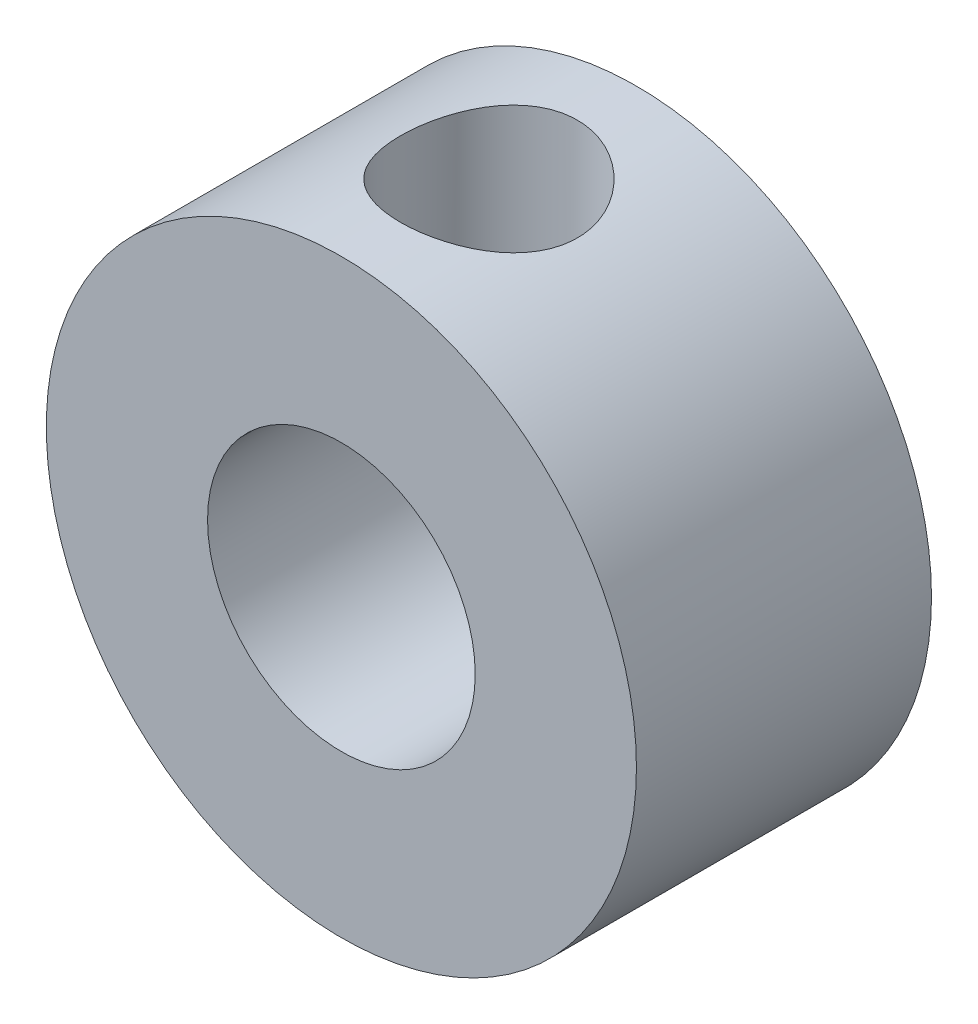
SolidWorks part; units mm, degrees
material "Plain Carbon Steel"
ref_plane "Front Plane" through (0, 0, 0) normal (0, 0, 1) x (1, 0, 0)
ref_plane "Top Plane" through (0, 0, 0) normal (0, 1, 0) x (1, 0, 0)
ref_plane "Right Plane" through (0, 0, 0) normal (1, 0, 0) x (0, 0, -1)
sketch "Sketch1" plane through (0, 0, 0) normal (0, 0, 1) x (1, 0, 0)
  circle A0 centre (0, 0) radius 3.175
  circle A1 centre (0, 0) radius 7
  dimension "D1" = 6.35
  dimension "D2" = 14
extrude "Boss-Extrude1" add sketch "Sketch1" along normal blind 7
ref_plane "Plane1" through (0, 7, 0) normal (0, 1, 0) x (1, 0, 0)
hole_wizard "M5x0.8 Tapped Hole1" positions "Sketch3" profile "Sketch2" tap size "M5x0.8" standard "ANSI Metric"
sketch "Sketch3" plane through (0, 7, 0) normal (0, 1, 0) x (1, 0, 0)
  line L0 (0, 0) -> (0, -7) construction
  line L1 (-7, -7) -> (7, -7) construction
  point P8 (0, -3.5)
sketch "Sketch2" plane through (0, 7, 3.5) normal (1, 0, 0) x (0, 0, 1)
  line L0 (0, 0) -> (0, 3.825)
  line L1 (0, 3.825) -> (2.1, 3.825)
  line L2 (2.1, 3.825) -> (2.1, 0)
  line L5 (2.1, 0) -> (0, 0)
  line L11 (0, -6.35) -> (0, 107.95) construction
  dimension "Thread Major Dia." = 4.2
  dimension "Thru Tap Drill Depth" = 3.825
